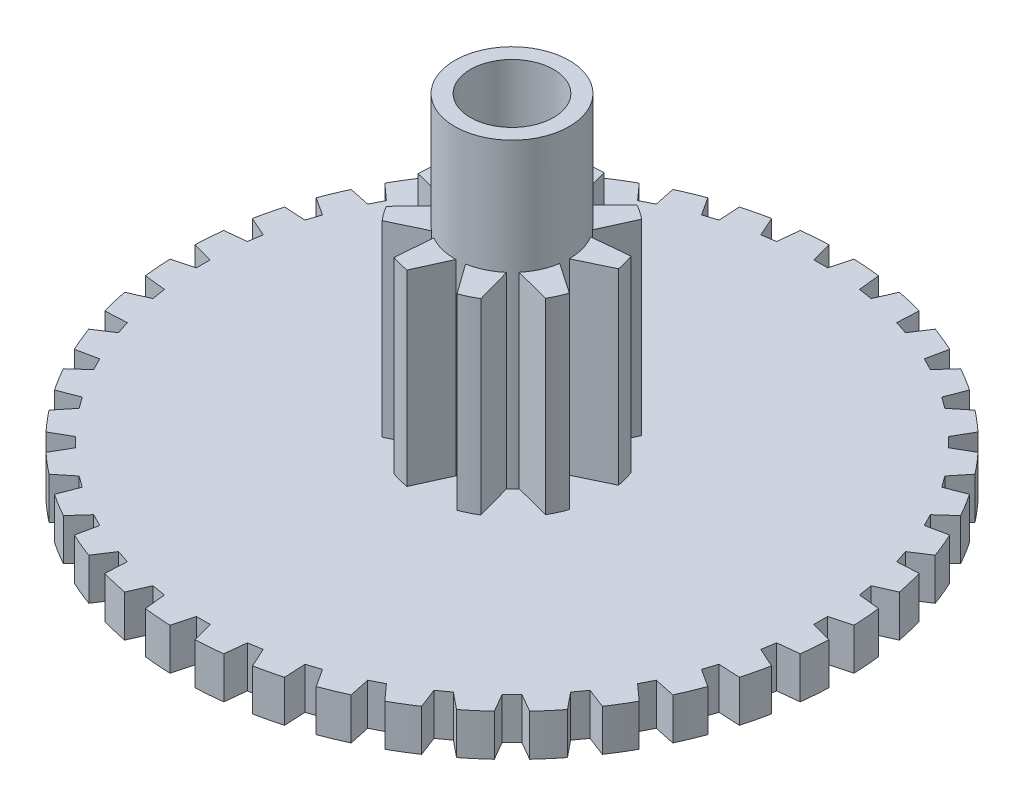
SolidWorks part; units mm, degrees
ref_plane "Front Plane" through (0, 0, 0) normal (0, 0, 1) x (1, 0, 0)
ref_plane "Top Plane" through (0, 0, 0) normal (0, 1, 0) x (1, 0, 0)
ref_plane "Right Plane" through (0, 0, 0) normal (1, 0, 0) x (0, 0, -1)
sketch "Sketch1" plane through (0, 0, 0) normal (0, 1, 0) x (1, 0, 0)
  line L0 (0, 4.75) -> (0, 0) construction
  line L1 (-0.18, 4.7466) -> (-0.1, 4.448)
  line L2 (-0.1, 4.448) -> (0.1, 4.448)
  line L3 (0.18, 4.7466) -> (0.1, 4.448)
  line L4 (0.5647, 4.7163) -> (0.5971, 4.4089)
  line L5 (0.5971, 4.4089) -> (0.7946, 4.3776)
  line L6 (0.9203, 4.66) -> (0.7946, 4.3776)
  line L7 (1.2956, 4.5699) -> (1.2794, 4.2612)
  line L8 (1.2794, 4.2612) -> (1.4696, 4.1994)
  line L9 (1.638, 4.4587) -> (1.4696, 4.1994)
  line L10 (1.9945, 4.311) -> (1.9303, 4.0086)
  line L11 (1.9303, 4.0086) -> (2.1085, 3.9178)
  line L12 (2.3153, 4.1475) -> (2.1085, 3.9178)
  line L13 (2.6444, 3.9459) -> (2.5336, 3.6573)
  line L14 (2.5336, 3.6573) -> (2.6954, 3.5397)
  line L15 (2.9356, 3.7343) -> (2.6954, 3.5397)
  line L16 (3.2291, 3.4836) -> (3.0745, 3.2159)
  line L17 (3.0745, 3.2159) -> (3.2159, 3.0745)
  line L18 (3.4836, 3.2291) -> (3.2159, 3.0745)
  line L19 (3.7343, 2.9356) -> (3.5397, 2.6954)
  line L20 (3.5397, 2.6954) -> (3.6573, 2.5336)
  line L21 (3.9459, 2.6444) -> (3.6573, 2.5336)
  line L22 (4.1475, 2.3153) -> (3.9178, 2.1085)
  line L23 (3.9178, 2.1085) -> (4.0086, 1.9303)
  line L24 (4.311, 1.9945) -> (4.0086, 1.9303)
  line L25 (4.4587, 1.638) -> (4.1994, 1.4696)
  line L26 (4.1994, 1.4696) -> (4.2612, 1.2794)
  line L27 (4.5699, 1.2956) -> (4.2612, 1.2794)
  line L28 (4.66, 0.9203) -> (4.3776, 0.7946)
  line L29 (4.3776, 0.7946) -> (4.4089, 0.5971)
  line L30 (4.7163, 0.5647) -> (4.4089, 0.5971)
  line L31 (4.7466, 0.18) -> (4.448, 0.1)
  line L32 (4.448, 0.1) -> (4.448, -0.1)
  line L33 (4.7466, -0.18) -> (4.448, -0.1)
  line L34 (4.7163, -0.5647) -> (4.4089, -0.5971)
  line L35 (4.4089, -0.5971) -> (4.3776, -0.7946)
  line L36 (4.66, -0.9203) -> (4.3776, -0.7946)
  line L37 (4.5699, -1.2956) -> (4.2612, -1.2794)
  line L38 (4.2612, -1.2794) -> (4.1994, -1.4696)
  line L39 (4.4587, -1.638) -> (4.1994, -1.4696)
  line L40 (4.311, -1.9945) -> (4.0086, -1.9303)
  line L41 (4.0086, -1.9303) -> (3.9178, -2.1085)
  line L42 (4.1475, -2.3153) -> (3.9178, -2.1085)
  line L43 (3.9459, -2.6444) -> (3.6573, -2.5336)
  line L44 (3.6573, -2.5336) -> (3.5397, -2.6954)
  line L45 (3.7343, -2.9356) -> (3.5397, -2.6954)
  line L46 (3.4836, -3.2291) -> (3.2159, -3.0745)
  line L47 (3.2159, -3.0745) -> (3.0745, -3.2159)
  line L48 (3.2291, -3.4836) -> (3.0745, -3.2159)
  line L49 (2.9356, -3.7343) -> (2.6954, -3.5397)
  line L50 (2.6954, -3.5397) -> (2.5336, -3.6573)
  line L51 (2.6444, -3.9459) -> (2.5336, -3.6573)
  line L52 (2.3153, -4.1475) -> (2.1085, -3.9178)
  line L53 (2.1085, -3.9178) -> (1.9303, -4.0086)
  line L54 (1.9945, -4.311) -> (1.9303, -4.0086)
  line L55 (1.638, -4.4587) -> (1.4696, -4.1994)
  line L56 (1.4696, -4.1994) -> (1.2794, -4.2612)
  line L57 (1.2956, -4.5699) -> (1.2794, -4.2612)
  line L58 (0.9203, -4.66) -> (0.7946, -4.3776)
  line L59 (0.7946, -4.3776) -> (0.5971, -4.4089)
  line L60 (0.5647, -4.7163) -> (0.5971, -4.4089)
  line L61 (0.18, -4.7466) -> (0.1, -4.448)
  line L62 (0.1, -4.448) -> (-0.1, -4.448)
  line L63 (-0.18, -4.7466) -> (-0.1, -4.448)
  line L64 (-0.5647, -4.7163) -> (-0.5971, -4.4089)
  line L65 (-0.5971, -4.4089) -> (-0.7946, -4.3776)
  line L66 (-0.9203, -4.66) -> (-0.7946, -4.3776)
  line L67 (-1.2956, -4.5699) -> (-1.2794, -4.2612)
  line L68 (-1.2794, -4.2612) -> (-1.4696, -4.1994)
  line L69 (-1.638, -4.4587) -> (-1.4696, -4.1994)
  line L70 (-1.9945, -4.311) -> (-1.9303, -4.0086)
  line L71 (-1.9303, -4.0086) -> (-2.1085, -3.9178)
  line L72 (-2.3153, -4.1475) -> (-2.1085, -3.9178)
  line L73 (-2.6444, -3.9459) -> (-2.5336, -3.6573)
  line L74 (-2.5336, -3.6573) -> (-2.6954, -3.5397)
  line L75 (-2.9356, -3.7343) -> (-2.6954, -3.5397)
  line L76 (-3.2291, -3.4836) -> (-3.0745, -3.2159)
  line L77 (-3.0745, -3.2159) -> (-3.2159, -3.0745)
  line L78 (-3.4836, -3.2291) -> (-3.2159, -3.0745)
  line L79 (-3.7343, -2.9356) -> (-3.5397, -2.6954)
  line L80 (-3.5397, -2.6954) -> (-3.6573, -2.5336)
  line L81 (-3.9459, -2.6444) -> (-3.6573, -2.5336)
  line L82 (-4.1475, -2.3153) -> (-3.9178, -2.1085)
  line L83 (-3.9178, -2.1085) -> (-4.0086, -1.9303)
  line L84 (-4.311, -1.9945) -> (-4.0086, -1.9303)
  line L85 (-4.4587, -1.638) -> (-4.1994, -1.4696)
  line L86 (-4.1994, -1.4696) -> (-4.2612, -1.2794)
  line L87 (-4.5699, -1.2956) -> (-4.2612, -1.2794)
  line L88 (-4.66, -0.9203) -> (-4.3776, -0.7946)
  line L89 (-4.3776, -0.7946) -> (-4.4089, -0.5971)
  line L90 (-4.7163, -0.5647) -> (-4.4089, -0.5971)
  line L91 (-4.7466, -0.18) -> (-4.448, -0.1)
  line L92 (-4.448, -0.1) -> (-4.448, 0.1)
  line L93 (-4.7466, 0.18) -> (-4.448, 0.1)
  line L94 (-4.7163, 0.5647) -> (-4.4089, 0.5971)
  line L95 (-4.4089, 0.5971) -> (-4.3776, 0.7946)
  line L96 (-4.66, 0.9203) -> (-4.3776, 0.7946)
  line L97 (-4.5699, 1.2956) -> (-4.2612, 1.2794)
  line L98 (-4.2612, 1.2794) -> (-4.1994, 1.4696)
  line L99 (-4.4587, 1.638) -> (-4.1994, 1.4696)
  line L100 (-4.311, 1.9945) -> (-4.0086, 1.9303)
  line L101 (-4.0086, 1.9303) -> (-3.9178, 2.1085)
  line L102 (-4.1475, 2.3153) -> (-3.9178, 2.1085)
  line L103 (-3.9459, 2.6444) -> (-3.6573, 2.5336)
  line L104 (-3.6573, 2.5336) -> (-3.5397, 2.6954)
  line L105 (-3.7343, 2.9356) -> (-3.5397, 2.6954)
  line L106 (-3.4836, 3.2291) -> (-3.2159, 3.0745)
  line L107 (-3.2159, 3.0745) -> (-3.0745, 3.2159)
  line L108 (-3.2291, 3.4836) -> (-3.0745, 3.2159)
  line L109 (-2.9356, 3.7343) -> (-2.6954, 3.5397)
  line L110 (-2.6954, 3.5397) -> (-2.5336, 3.6573)
  line L111 (-2.6444, 3.9459) -> (-2.5336, 3.6573)
  line L112 (-2.3153, 4.1475) -> (-2.1085, 3.9178)
  line L113 (-2.1085, 3.9178) -> (-1.9303, 4.0086)
  line L114 (-1.9945, 4.311) -> (-1.9303, 4.0086)
  line L115 (-1.638, 4.4587) -> (-1.4696, 4.1994)
  line L116 (-1.4696, 4.1994) -> (-1.2794, 4.2612)
  line L117 (-1.2956, 4.5699) -> (-1.2794, 4.2612)
  line L118 (-0.9203, 4.66) -> (-0.7946, 4.3776)
  line L119 (-0.7946, 4.3776) -> (-0.5971, 4.4089)
  line L120 (-0.5647, 4.7163) -> (-0.5971, 4.4089)
  circle A0 centre (0, 0) radius 4.75
  point P9 (0, 4.448)
  point P168 (0, 0)
  dimension "D1" = 9.5
  dimension "D4" = 0.18
  dimension "D2" = 15
  dimension "D3" = 0.2
  dimension "D5" = 40
extrude "Boss-Extrude1" add sketch "Sketch1" along normal blind 0.6 contours L61 A0 L60 L59 L58 L57 L56 L55 L54 L53 L52 L51 L50 L49 L48 L47 L46 L45 L44 L43 L42 L41 L40 L39 L38 L37 L36 L35 L34 L33 L32 L31 L30 L29 L28 L27 L26 L25 L24
sketch "Sketch2" plane through (0, 0.6, 0) normal (0, 1, 0) x (1, 0, 0)
  line L0 (0, 0) -> (0.3299, 1.2833) construction
  line L1 (0, 1.325) -> (0.1504, 0.7857)
  line L2 (0.1504, 0.7857) -> (0.2472, 0.7608)
  line L3 (0.6391, 1.1607) -> (0.2472, 0.7608)
  line L4 (0.8517, 1.015) -> (0.6203, 0.5052)
  line L5 (0.6203, 0.5052) -> (0.6784, 0.4239)
  line L6 (1.2356, 0.4784) -> (0.6784, 0.4239)
  line L7 (1.3049, 0.2301) -> (0.7999, -0.0117)
  line L8 (0.7999, -0.0117) -> (0.7922, -0.1114)
  line L9 (1.254, -0.4278) -> (0.7922, -0.1114)
  line L10 (1.1475, -0.6625) -> (0.6053, -0.5231)
  line L11 (0.6053, -0.5231) -> (0.5353, -0.5945)
  line L12 (0.6857, -1.1338) -> (0.5353, -0.5945)
  line L13 (0.4532, -1.2451) -> (0.1274, -0.7898)
  line L14 (0.1274, -0.7898) -> (0.0279, -0.7995)
  line L15 (-0.2035, -1.3093) -> (0.0279, -0.7995)
  line L16 (-0.4532, -1.2451) -> (-0.4101, -0.6869)
  line L17 (-0.4101, -0.6869) -> (-0.4925, -0.6304)
  line L18 (-0.9975, -0.8721) -> (-0.4925, -0.6304)
  line L19 (-1.1475, -0.6625) -> (-0.7557, -0.2626)
  line L20 (-0.7557, -0.2626) -> (-0.7825, -0.1663)
  line L21 (-1.3247, -0.0269) -> (-0.7825, -0.1663)
  line L22 (-1.3049, 0.2301) -> (-0.7477, 0.2845)
  line L23 (-0.7477, 0.2845) -> (-0.7063, 0.3756)
  line L24 (-1.0321, 0.8309) -> (-0.7063, 0.3756)
  line L25 (-0.8517, 1.015) -> (-0.3899, 0.6986)
  line L26 (-0.3899, 0.6986) -> (-0.2997, 0.7418)
  line L27 (-0.2565, 1.2999) -> (-0.2997, 0.7418)
  circle A0 centre (0, 0) radius 1.325
  circle A1 centre (0, 0) radius 0.8
  point P9 (0.1988, 0.7733)
  point P45 (0, 0)
  dimension "D1" = 2.65
  dimension "D4" = 1.6
  dimension "D2" = 30
  dimension "D3" = 0.1
  dimension "D5" = 9
extrude "Boss-Extrude2" add sketch "Sketch2" along normal blind 2.7
sketch "Sketch3" plane through (0, 0.6, 0) normal (0, 1, 0) x (1, 0, 0)
  circle A0 centre (0, 0) radius 1.325
  arc A1 (1.3049, 0.2301) -> (1.2356, 0.4784) centre (0, 0) ccw construction
sketch "Sketch4" plane through (0, 3.3, 0) normal (0, 1, 0) x (1, 0, 0)
  circle A0 centre (0, 0) radius 0.825
  dimension "D1" = 1.65
extrude "Boss-Extrude4" add sketch "Sketch4" along normal blind 1.65 and the other way blind 4.25
extrude "Boss-Extrude5" add sketch "Sketch3" against normal blind 1
sketch "Sketch5" plane through (0, 4.95, 0) normal (0, 1, 0) x (1, 0, 0)
  circle A0 centre (0, 0) radius 0.6
  dimension "D1" = 1.2
extrude "Cut-Extrude1" cut sketch "Sketch5" against normal blind 6
